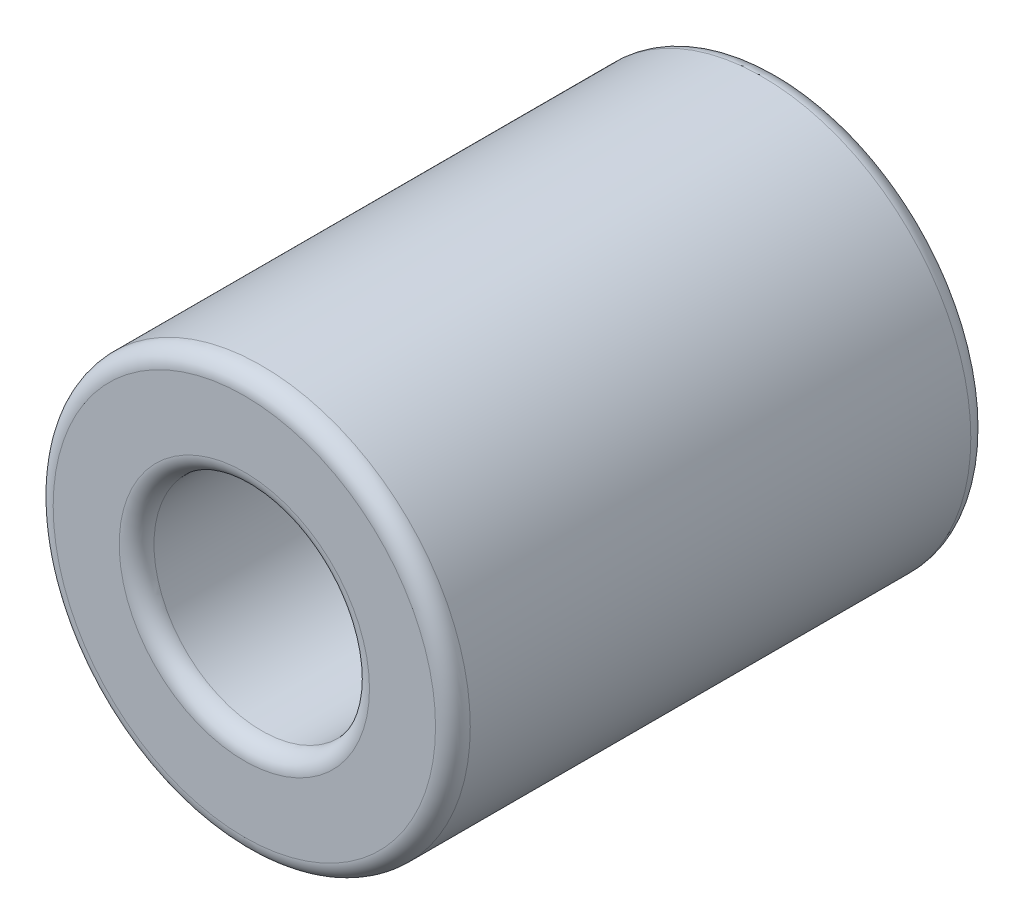
SolidWorks part; units mm, degrees
material "PMMA"
ref_plane "Přední rovina" through (0, 0, 0) normal (0, 0, 1) x (1, 0, 0)
ref_plane "Horní rovina" through (0, 0, 0) normal (0, 1, 0) x (1, 0, 0)
ref_plane "Pravá rovina" through (0, 0, 0) normal (1, 0, 0) x (0, 0, -1)
sketch "Skica2" plane through (0, 0, 0) normal (0, 0, 1) x (1, 0, 0)
  circle A0 centre (0, 0) radius 3
  circle A1 centre (0, 0) radius 1.55
  dimension "D1" = 6
  dimension "D2" = 3.1
extrude "Přidat vysunutím1" add sketch "Skica2" along normal blind 7.7
fillet "Zaoblit1" radius 0.25 4 edges at (1.55, 0, 0) (1.55, 0, 7.7) (3, 0, 0) (3, 0, 7.7)
